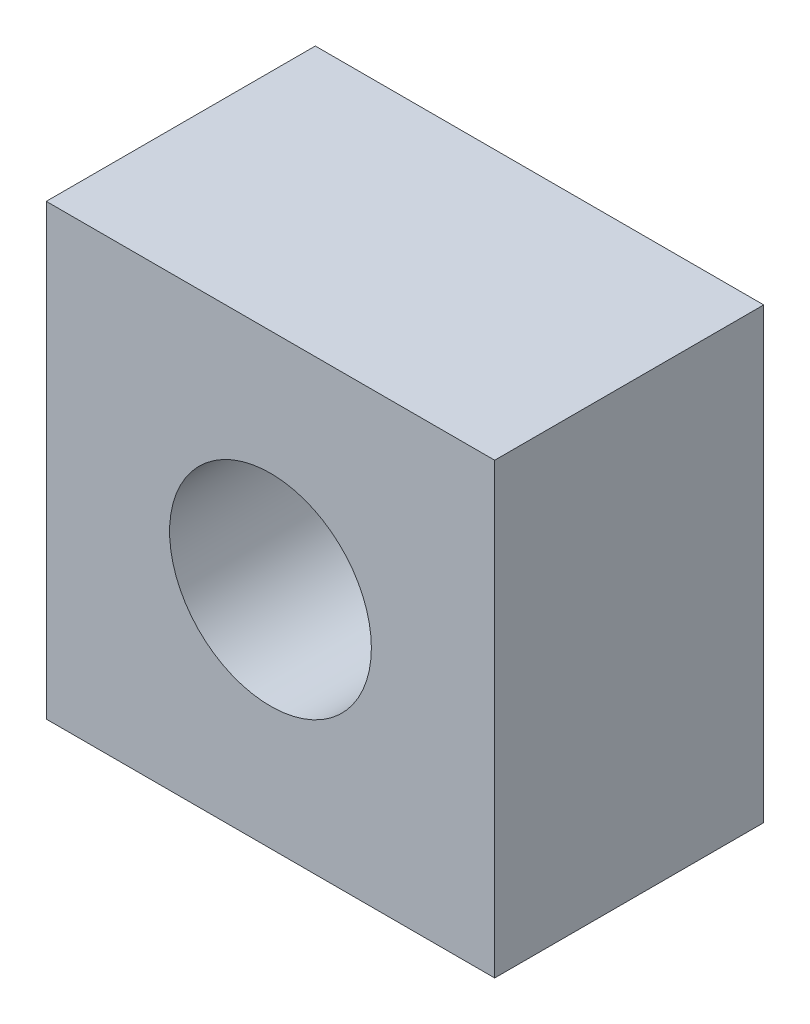
SolidWorks part; units mm, degrees
ref_plane "Front Plane" through (0, 0, 0) normal (0, 0, 1) x (1, 0, 0)
ref_plane "Top Plane" through (0, 0, 0) normal (0, 1, 0) x (1, 0, 0)
ref_plane "Right Plane" through (0, 0, 0) normal (1, 0, 0) x (0, 0, -1)
sketch "Sketch1" plane through (0, 0, 0) normal (0, 0, 1) x (1, 0, 0)
  line L1 (-10, 10) -> (10, 10)
  line L2 (-10, 10) -> (-10, -10)
  line L3 (-10, -10) -> (10, -10)
  line L4 (10, 10) -> (10, -10)
  circle A0 centre (0, 0) radius 4.5
  dimension "D1" = 9
  dimension "D2" = 20
  dimension "D3" = 20
  dimension "D4" = 10
  dimension "D5" = 10
extrude "Boss-Extrude1" add sketch "Sketch1" along normal blind 10 contours A0 | L1 L4 L3 L2
sketch "Sketch2" plane through (0, 0, 0) normal (0, 0, 1) x (1, 0, 0)
  line L1 (-10, 10) -> (10, 10)
  line L2 (-10, 10) -> (-10, -10)
  line L3 (-10, -10) -> (10, -10)
  line L4 (10, 10) -> (10, -10)
extrude "Boss-Extrude2" add sketch "Sketch2" against normal blind 2
